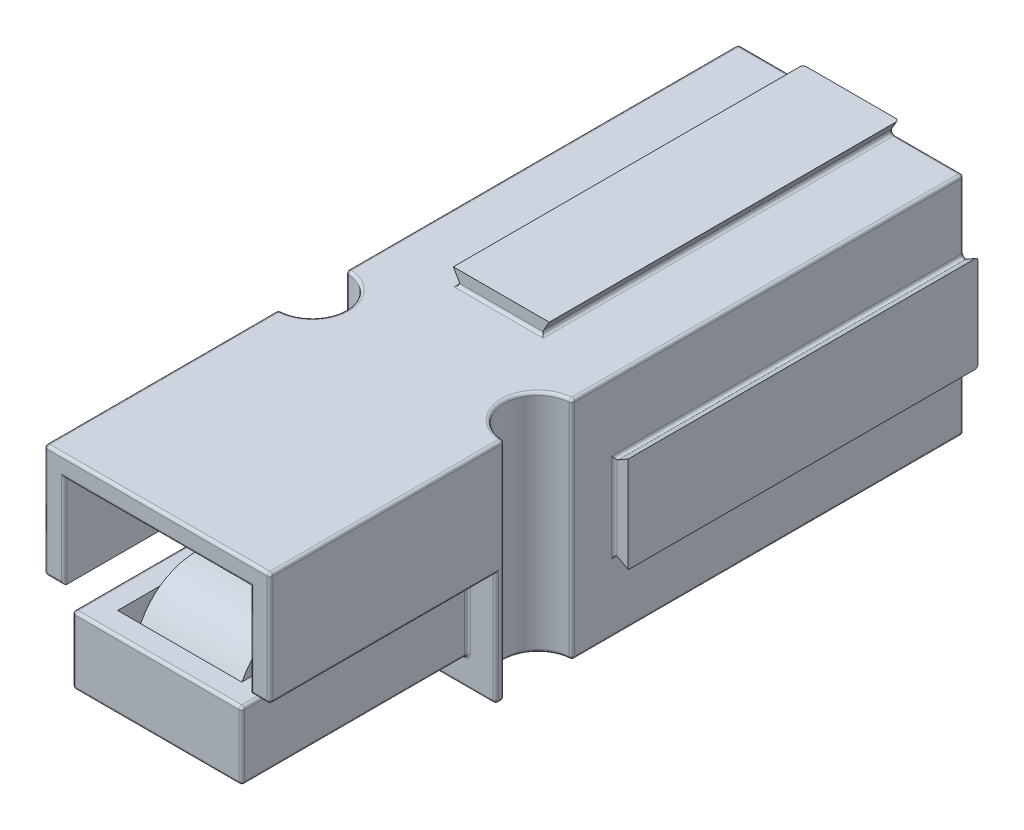
SolidWorks part; units mm, degrees
material "ABS"
ref_plane "Face" through (0, 0, 0) normal (0, 0, 1) x (1, 0, 0)
ref_plane "Dessus" through (0, 0, 0) normal (0, 1, 0) x (1, 0, 0)
ref_plane "Droite" through (0, 0, 0) normal (1, 0, 0) x (0, 0, -1)
sketch "Esquisse1" plane through (0, 0, 0) normal (0, 0, 1) x (1, 0, 0)
  line L1 (-4.25, 4.25) -> (4.25, 4.25)
  line L2 (-4.25, 4.25) -> (-4.25, -4.25)
  line L3 (-4.25, -4.25) -> (4.25, -4.25)
  line L4 (4.25, 4.25) -> (4.25, -4.25)
  point P4 (0, 4.25)
  point P6 (-4.25, 0)
  dimension "D1" = 8.5
  dimension "D2" = 8.5
extrude "Extrusion1" add sketch "Esquisse1" along normal blind 24.6
sketch "Esquisse6" plane through (0, 0, 24.6) normal (0, 0, 1) x (1, 0, 0)
  line L0 (-4.25, 4.25) -> (-4.25, -4.25) construction
  line L2 (4.5005, 4.25) -> (4.5005, 3.75)
  line L3 (-4.25, 4.25) -> (-1.95, 4.25)
  line L4 (-4.25, 4.25) -> (-4.25, 3.75)
  line L5 (-4.25, 3.75) -> (-1.95, 3.75)
  line L6 (-1.95, 4.25) -> (-1.95, 3.75)
  line L7 (4.5005, 4.25) -> (1.45, 4.25)
  line L8 (1.45, 4.25) -> (1.45, 3.75)
  line L9 (4.5005, 3.75) -> (1.45, 3.75)
  dimension "D1" = 3.4
  dimension "D2" = 0.5
  dimension "D3" = 2.3
extrude "Enlèv. mat.-Extru.4" cut sketch "Esquisse6" against normal through all
sketch "Esquisse2" plane through (0, 0, 24.6) normal (0, 0, 1) x (1, 0, 0)
  line L0 (1.45, 4.25) -> (-1.95, 4.25) construction
  line L2 (-4.25, -4.25) -> (4.25, -4.25) construction
  line L8 (4.25, 1.45) -> (4.25, 4.25)
  line L12 (4.25, 4.25) -> (3.75, 4.25)
  line L13 (4.25, -4.25) -> (3.75, -4.25)
  line L14 (4.25, -4.25) -> (4.25, -1.95)
  line L15 (4.25, -1.95) -> (3.75, -1.95)
  line L16 (3.75, -4.25) -> (3.75, -1.95)
  line L18 (4.25, 1.45) -> (3.75, 1.45)
  line L19 (3.75, 4.25) -> (3.75, 1.45)
  dimension "D1" = 2.3
  dimension "D3" = 0.5
  dimension "D4" = 3.4
extrude "Enlèv. mat.-Extru.1" cut sketch "Esquisse2" against normal through all
sketch "Esquisse4" plane through (0, 3.75, 0) normal (0, 1, 0) x (-1, 0, 0)
  line L0 (0.25, 24.6) -> (0.25, 9.1927) construction
  line L6 (4.25, 24.6) -> (1.95, 24.6) construction
  circle A0 centre (-3.75, 15.1) radius 1.2
  circle A1 centre (4.25, 15.1) radius 1.2
  dimension "D1" = 2.4
  dimension "D2" = 9.5
extrude "Enlèv. mat.-Extru.3" cut sketch "Esquisse4" against normal through all
sketch "Esquisse11" plane through (0, 0, 24.6) normal (0, 0, 1) x (1, 0, 0)
  line L1 (-1.95, 4.25) -> (1.45, 4.25)
  line L2 (-1.95, 4.25) -> (-1.95, 3.75)
  line L3 (-1.95, 3.75) -> (1.45, 3.75)
  line L4 (1.45, 4.25) -> (1.45, 3.75)
  line L5 (4.25, 1.45) -> (3.75, 1.45)
  line L6 (4.25, 1.45) -> (4.25, -1.95)
  line L7 (4.25, -1.95) -> (3.75, -1.95)
  line L8 (3.75, 1.45) -> (3.75, -1.95)
extrude "Enlèv. mat.-Extru.9" cut sketch "Esquisse11" against normal blind 12.2
sketch "Esquisse5" plane through (0, 0, 24.6) normal (0, 0, 1) x (1, 0, 0)
  line L0 (-0.25, 3.75) -> (-0.25, -5.3524) construction
  line L1 (-4.25, -4.25) -> (3.75, -4.25) construction
  line L2 (-4.25, -0.25) -> (-3.25, -0.25)
  line L3 (-4.25, 3.75) -> (-4.25, -4.25) construction
  line L4 (-3.25, -0.25) -> (-3.25, -3.25)
  line L5 (-3.25, -3.25) -> (2.75, -3.25)
  line L6 (-4.25, 3.75) -> (3.75, 3.75) construction
  line L7 (-4.25, -0.25) -> (-4.25, -4.25)
  line L8 (-4.25, -4.25) -> (3.75, -4.25) construction
  line L9 (-4.25, -4.25) -> (3.75, -4.25) construction
  line L10 (2.75, -0.25) -> (2.75, -3.25)
  line L11 (3.75, -0.25) -> (2.75, -0.25)
  line L12 (3.75, -0.25) -> (3.75, -4.25)
  line L13 (-4.25, -4.25) -> (3.75, -4.25)
  point P19 (-0.25, -3.25)
  point P22 (-0.25, -4.25)
  dimension "D1" = 1
  dimension "D2" = 1
  dimension "D3" = 4
extrude "Enlèv. mat.-Extru.5" cut sketch "Esquisse5" against normal blind 8
sketch "Esquisse7" plane through (0, 0, 24.6) normal (0, 0, 1) x (1, 0, 0)
  line L5 (2.75, -0.85) -> (-3.25, -0.85)
  line L8 (-4.25, 3.05) -> (3.75, 3.05)
  line L9 (-3.55, 3.05) -> (3.05, 3.05)
  line L11 (-3.55, 3.75) -> (-3.55, -0.25)
  line L12 (3.05, -0.85) -> (-3.55, -0.85)
  line L24 (-3.55, 3.05) -> (-3.55, -0.85)
  line L26 (3.05, 3.75) -> (3.05, -0.25)
  line L27 (3.05, 3.05) -> (3.05, -0.85)
  dimension "D1" = 0.7
  dimension "D2" = 2.4
  dimension "D3" = 0.7
  dimension "D4" = 0.7
extrude "Enlèv. mat.-Extru.6" cut sketch "Esquisse7" against normal up to surface (8 mm away) up to face at (-0.25, -2, 16.6)
sketch "Esquisse8" plane through (0, 0, 0) normal (0, 0, -1) x (-1, 0, 0)
  line L37 (2.85, 3.75) -> (2.85, -4.25)
  line L38 (2.85, 2.35) -> (2.85, -2.85)
  line L40 (-2.35, -1.95) -> (-2.35, -4.25)
  line L41 (-2.35, 2.35) -> (-2.35, -2.85)
  line L43 (4.25, -2.85) -> (-3.75, -2.85)
  line L44 (2.85, -2.85) -> (-2.35, -2.85)
  line L46 (-1.45, 2.35) -> (-3.75, 2.35)
  line L47 (2.85, 2.35) -> (-2.35, 2.35)
  dimension "D1" = 1.4
  dimension "D2" = 1.4
  dimension "D3" = 1.4
  dimension "D4" = 1.4
extrude "Enlèv. mat.-Extru.7" cut sketch "Esquisse8" against normal blind 8
sketch "Esquisse9" plane through (0, 0, 0) normal (0, 0, -1) x (-1, 0, 0)
  line L0 (0.25, 4.25) -> (0.25, 3.6866) construction
  line L1 (-1.45, 4.25) -> (1.95, 4.25) construction
  line L2 (-1.45, 4.25) -> (-1.1613, 3.75)
  line L4 (-1.1613, 3.75) -> (-1.45, 3.75)
  line L5 (-1.45, 3.75) -> (-1.45, 4.25)
  line L6 (1.95, 3.75) -> (1.95, 4.25)
  line L7 (1.6613, 3.75) -> (1.95, 3.75)
  line L8 (1.95, 4.25) -> (1.6613, 3.75)
  line L9 (-4.25, -1.95) -> (-3.75, -1.95) construction
  line L10 (-4.25, 1.45) -> (-3.75, 1.1613)
  line L12 (-3.75, 1.1613) -> (-3.75, 1.45)
  line L13 (-3.75, 1.45) -> (-4.25, 1.45)
  line L14 (-3.75, -1.95) -> (-4.25, -1.95)
  line L15 (-3.75, -1.6613) -> (-3.75, -1.95)
  line L16 (-4.25, -1.95) -> (-3.75, -1.6613)
  dimension "D1" = 60
  dimension "D2" = 60
extrude "Enlèv. mat.-Extru.8" cut sketch "Esquisse9" against normal blind 13
sketch "Esquisse10" plane through (0, 0, 0) normal (0, 0, -1) x (-1, 0, 0)
  line L0 (4.25, -0.25) -> (-4.8932, -0.25) construction
  line L1 (4.25, 3.75) -> (4.25, -4.25) construction
sketch "Esquisse12" plane through (0, 0, 0) normal (0, 0, -1) x (-1, 0, 0)
  line L3 (4.25, 1.1613) -> (4.25, -1.6613)
  line L6 (4.25, -1.6613) -> (3.75, -1.95)
  line L7 (3.75, -1.95) -> (3.75, 1.45)
  line L8 (3.75, 1.45) -> (4.25, 1.1613)
  line L10 (-1.1613, -4.25) -> (1.6613, -4.25)
  line L13 (1.95, -3.75) -> (1.6613, -4.25)
  line L14 (-1.45, -3.75) -> (1.95, -3.75)
  line L15 (-1.1613, -4.25) -> (-1.45, -3.75)
extrude "Enlèv. mat.-Extru.10" cut sketch "Esquisse12" against normal up to surface (12.4 mm away) up to face at (-0.25, 4, 12.4)
ref_plane "Plan1" through (-0.25, 0, 0) normal (1, 0, 0) x (0, 0, -1)
sketch "Esquisse14" plane through (0, -0.85, 0) normal (0, 1, 0) x (-1, 0, 0)
  line L8 (2.45, 23.8) -> (-1.95, 23.8)
  line L9 (-1.95, 23.8) -> (-1.95, 17.4)
  line L10 (-1.95, 17.4) -> (2.45, 17.4)
  line L11 (2.45, 17.4) -> (2.45, 23.8)
  line L12 (2.45, 23.8) -> (-1.95, 23.8)
  line L13 (-1.95, 23.8) -> (-1.95, 17.4)
  line L14 (-1.95, 17.4) -> (2.45, 17.4)
  line L15 (2.45, 17.4) -> (2.45, 23.8)
  dimension "D1" = 0.8
extrude "Enlèv. mat.-Extru.11" cut sketch "Esquisse14" against normal blind 1.75
sketch "Esquisse15" plane through (0, 0, 17.4) normal (0, 0, 1) x (1, 0, 0)
  line L4 (1.95, -0.85) -> (-2.45, -0.85)
  line L5 (-2.45, -0.85) -> (-2.45, -2.6)
  line L6 (-2.45, -2.6) -> (1.95, -2.6)
  line L7 (1.95, -2.6) -> (1.95, -0.85)
  line L8 (1.95, -0.85) -> (-2.45, -0.85)
  line L9 (-2.45, -0.85) -> (-2.45, -2.6)
  line L10 (-2.45, -2.6) -> (1.95, -2.6)
  line L11 (1.95, -2.6) -> (1.95, -0.85)
  dimension "D1" = 0
extrude "Enlèv. mat.-Extru.12" cut sketch "Esquisse15" against normal up to surface (0.8 mm away) up to face at (-0.25, -0.425, 16.6)
sketch "Esquisse16" plane through (0, 0, 0) normal (0, 0, -1) x (-1, 0, 0)
  line L0 (0.25, 2.35) -> (0.25, -2.85) construction
  line L1 (2.85, 2.35) -> (-2.35, 2.35) construction
  line L2 (-2.35, -2.85) -> (2.85, -2.85) construction
  line L3 (2.85, -0.25) -> (-2.35, -0.25) construction
  line L4 (2.85, -2.85) -> (2.85, 2.35) construction
  line L5 (4.25, -0.25) -> (-4.8932, -0.25) construction
  circle A0 centre (0.25, -0.25) radius 2.6
fillet "Fillet1" radius 0.1 70 edges at (-4.25, 2.4557, 0) (-4.25, 1.75, 24.6) (-4.25, -4.25, 16.45) (-4.25, -2.25, 16.6) (-4.25, -0.25, 20.6) (-3.25, -2.05, 16.6) (-0.25, -3.25, 16.6) (-3.25, -3.25, 20.6) (2.75, -3.25, 20.6) (3.75, -2.25, 16.6) (3.75, -0.25, 20.6) (-0.25, -4.25, 16.6) (3.4, -0.25, 24.6) (-0.25, -3.25, 24.6) (-3.25, -2.05, 24.6) (2.75, -2.05, 16.6) (-4.25, 3.75, 6.95) (2.75, -2.05, 24.6) (-3.9, -0.25, 24.6) (-0.25, -0.85, 24.6) (3.05, 1.4, 24.6) (-0.25, 3.05, 24.6) (-3.55, 1.4, 24.6) (2.35, -0.85, 16.6) (-3.25, -0.85, 20.6) (2.75, -0.85, 20.6) (-2.9557, 3.75, 0) (-0.25, 3.75, 24.6) (-0.25, 2.35, 0) (2.35, -0.25, 0) (-0.25, -2.85, 0) (-2.85, -0.25, 0) (1.1613, 3.75, 6.2) (1.3057, 4, 0) (-0.25, 3.75, 12.4) (-1.6613, 3.75, 6.2) (-1.8057, 4, 0) (3.75, -0.25, 12.4) (3.75, 1.1613, 6.2) (4, 1.3057, 0) (3.75, -1.6613, 6.2) (4, -1.8057, 0) (-4.25, -2.9557, 0) (-4.25, -1.6613, 6.2) (-4.25, -0.25, 12.4) (-4.25, 1.1613, 6.2) (2.4557, -4.25, 0) (1.1613, -4.25, 6.2) (-0.25, -4.25, 12.4) (-1.6613, -4.25, 6.2) (2.4557, 3.75, 0) (-2.85, -0.85, 16.6) (3.75, 3.75, 20.45) (-2.9557, -4.25, 0) (3.75, 2.4557, 0) (3.75, 1.75, 24.6) (3.75, -2.9557, 0) (3.75, -4.25, 6.95) (3.75, -4.25, 16.45) (3.75, 3.75, 6.95) (2.55, 3.75, 15.1) (3.75, -0.25, 16.3) (3.75, -0.25, 13.9) (2.55, -4.25, 15.1) (-4.25, 3.75, 20.45) (-3.05, 3.75, 15.1) (-4.25, -4.25, 6.95) (-3.05, -4.25, 15.1) (-4.25, -0.25, 13.9) (-4.25, -0.25, 16.3)
sketch "Sketch1" plane through (0, 0, 8) normal (0, 0, -1) x (-1, 0, 0)
  line L0 (0.25, -0.25) -> (0.25, 2.35) construction
  line L1 (2.85, 2.35) -> (-2.35, 2.35) construction
  line L2 (0.25, -0.25) -> (2.85, -0.25) construction
  line L3 (2.85, -2.85) -> (2.85, 2.35) construction
  line L4 (0.25, -0.25) -> (0.25, -2.85) construction
  line L5 (-2.35, -2.85) -> (2.85, -2.85) construction
  line L6 (0.25, -0.25) -> (-2.35, -0.25) construction
  line L7 (-2.35, 2.35) -> (-2.35, -2.85) construction
  circle A0 centre (0.25, -0.25) radius 2
  dimension "D1" = 4
extrude "Cut-Extrude1" cut sketch "Sketch1" against normal offset from surface (7.6 mm away) 1 up to face at (-0.25, -0.4, 16.6)
scale "Scale1" bodies to scale 117 118 scale about centroid uniform scaling yes scale factor 1.95
sketch "Esquisse13" plane through (-0.25, 0, 0) normal (1, 0, 0) x (0, 0, -1)
  line L0 (-30.1203, -0.2252) -> (-22.142, -3.3971)
  line L1 (-22.142, -8.3327) -> (-22.142, -0.5327) construction
  line L2 (-30.342, -0.7827) -> (-22.142, -4.0427)
  line L3 (-35.176, -2.9827) -> (-35.742, -2.7837)
  line L4 (-22.142, -4.0427) -> (-22.142, -3.3971)
  line L5 (-30.342, -0.7827) -> (-22.3637, -3.9546) construction
  line L6 (-22.142, -1.7027) -> (-22.142, -6.3827) construction
  line L7 (-37.742, -1.7027) -> (-37.742, -6.3827) construction
  line L9 (-22.142, -6.3827) -> (-37.742, -6.3827) construction
  arc A0 (-35.742, -2.7837) -> (-30.1203, -0.2252) centre (-31.7023, -4.2045) cw
  arc A1 (-35.176, -2.9827) -> (-30.342, -0.7827) centre (-31.7023, -4.2045) cw
  point P17 (0, 0)
  dimension "D2" = 2
  dimension "D3" = 5.6
  dimension "D4" = 3.4
  dimension "D5" = 7.4
  dimension "D1" = 0.6
extrude "Extrusion2" add sketch "Esquisse13" along normal mid plane 7
